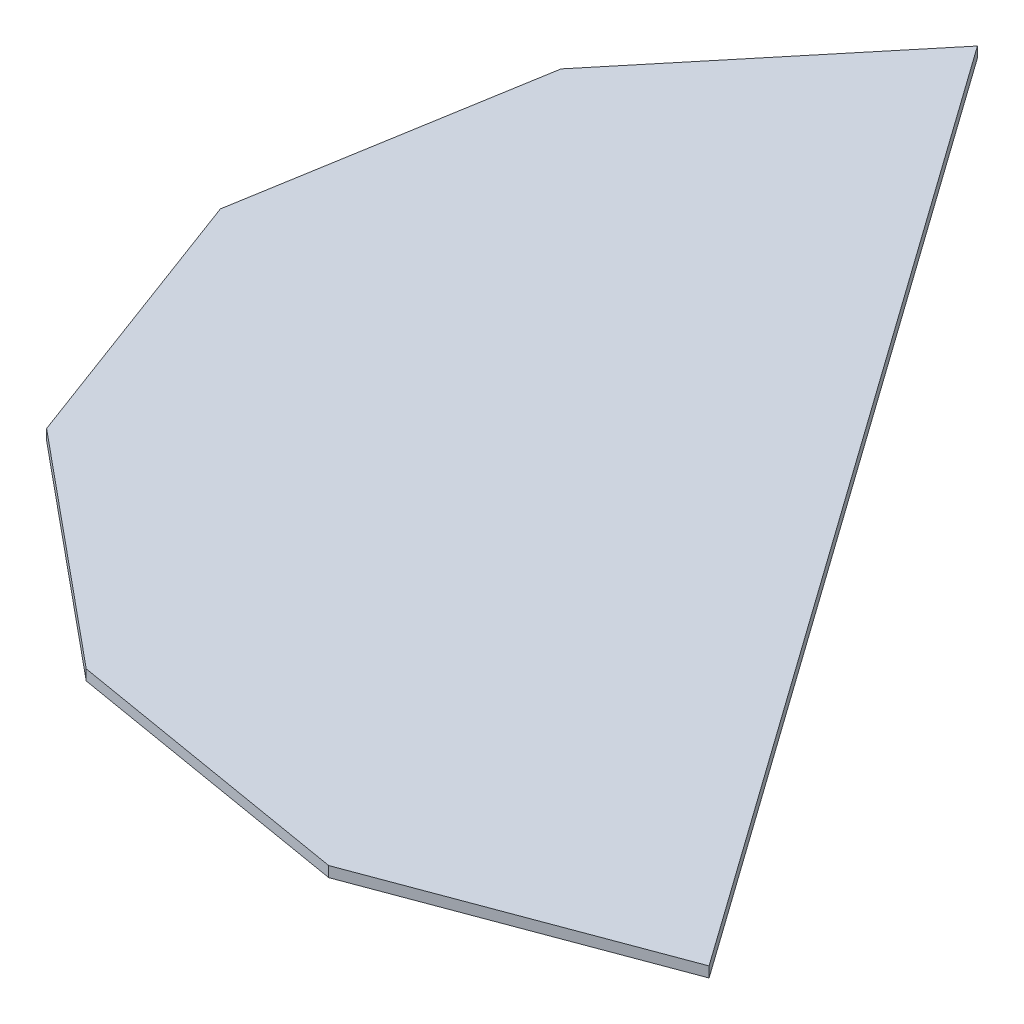
SolidWorks part; units mm, degrees
ref_plane "Front Plane" through (0, 0, 0) normal (0, 0, 1) x (1, 0, 0)
ref_plane "Top Plane" through (0, 0, 0) normal (0, 1, 0) x (1, 0, 0)
ref_plane "Right Plane" through (0, 0, 0) normal (1, 0, 0) x (0, 0, -1)
sketch "Sketch1" plane through (0, 0, 0) normal (0, 1, 0) x (1, 0, 0)
  line L0 (-151.7135, -14.4489) -> (-124.1633, -88.3699)
  line L5 (-88.3699, 124.1633) -> (-138.6122, 63.3436)
  line L6 (-138.6122, 63.3436) -> (-151.7135, -14.4489)
  line L7 (-124.1633, -88.3699) -> (-63.3436, -138.6122)
  line L8 (-63.3436, -138.6122) -> (14.4489, -151.7135)
  line L9 (14.4489, -151.7135) -> (88.3699, -124.1633)
  line L12 (-88.3699, 124.1633) -> (88.3699, -124.1633)
  line L14 (-14.4489, 151.7135) -> (-38.4132, 142.782) [skipped]
  line L15 (63.3436, 138.6122) -> (24.4474, 145.1629) [skipped]
  line L16 (124.1633, 88.3699) -> (93.7535, 113.491) [skipped]
  line L17 (151.7135, 14.4489) -> (137.9384, 51.4094) [skipped]
  line L18 (113.491, -93.7535) -> (138.6122, -63.3436) [skipped]
  line L19 (138.6122, -63.3436) -> (145.1629, -24.4474) [skipped]
  arc A0 (-85.3587, 119.9325) -> (85.3587, -119.9325) centre (0, 0) ccw construction
  dimension "D1" = 304.8
extrude "Boss-Extrude1" add sketch "Sketch1" along normal blind 2.794
